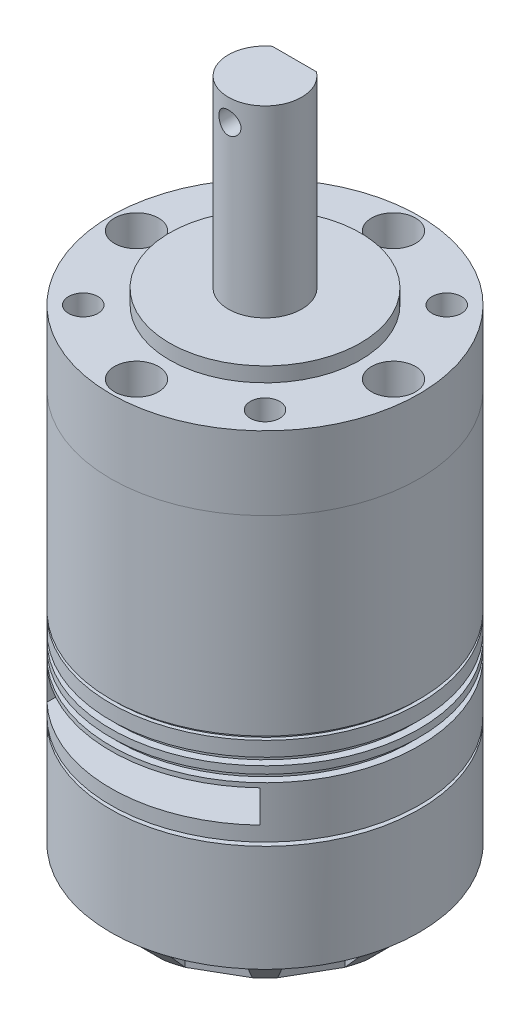
SolidWorks part; units mm, degrees
ref_plane "前视基准面" through (0, 0, 0) normal (0, 0, 1) x (1, 0, 0)
ref_plane "上视基准面" through (0, 0, 0) normal (0, 1, 0) x (1, 0, 0)
ref_plane "右视基准面" through (0, 0, 0) normal (1, 0, 0) x (0, 0, -1)
sketch "草图1" plane through (0, 0, 0) normal (0, 1, 0) x (1, 0, 0)
  circle A0 centre (0, 0) radius 21
  dimension "D1" = 42
extrude "凸台-拉伸1" add sketch "草图1" along normal blind 31
chamfer "倒角1" distance 3.5 angle 45 1 edges at (0, 0, 21)
sketch "草图2" plane through (0, 0, 0) normal (0, -1, 0) x (1, 0, 0)
  line L0 (3.35, -17.1764) -> (-3.35, -17.1764)
  line L1 (-3.35, -17.1764) -> (-3.85, -20.6441)
  line L2 (-3.85, -20.6441) -> (3.85, -20.6441) construction
  line L3 (3.85, -20.6441) -> (3.35, -17.1764)
  line L4 (-3.85, -20.6441) -> (-3.85, -22.4949)
  line L5 (-3.85, -22.4949) -> (3.85, -22.4949)
  line L6 (3.85, -22.4949) -> (3.85, -20.6441)
  line L7 (-6.9878, -19.8033) -> (-5.687, -16.5502)
  line L8 (-5.687, -16.5502) -> (-11.4894, -13.2002)
  line L9 (-11.4894, -13.2002) -> (-13.6562, -15.9533)
  line L10 (-13.6562, -15.9533) -> (-14.5816, -17.5562)
  line L11 (-14.5816, -17.5562) -> (-7.9133, -21.4062)
  line L12 (-7.9133, -21.4062) -> (-6.9878, -19.8033)
  line L13 (-13.6562, -15.9533) -> (-6.9878, -19.8033) construction
  line L14 (-15.9533, -13.6562) -> (-13.2002, -11.4894)
  line L15 (-13.2002, -11.4894) -> (-16.5502, -5.687)
  line L16 (-16.5502, -5.687) -> (-19.8033, -6.9878)
  line L17 (-19.8033, -6.9878) -> (-21.4062, -7.9133)
  line L18 (-21.4062, -7.9133) -> (-17.5562, -14.5816)
  line L19 (-17.5562, -14.5816) -> (-15.9533, -13.6562)
  line L20 (-19.8033, -6.9878) -> (-15.9533, -13.6562) construction
  line L21 (-20.6441, -3.85) -> (-17.1764, -3.35)
  line L22 (-17.1764, -3.35) -> (-17.1764, 3.35)
  line L23 (-17.1764, 3.35) -> (-20.6441, 3.85)
  line L24 (-20.6441, 3.85) -> (-22.4949, 3.85)
  line L25 (-22.4949, 3.85) -> (-22.4949, -3.85)
  line L26 (-22.4949, -3.85) -> (-20.6441, -3.85)
  line L27 (-20.6441, 3.85) -> (-20.6441, -3.85) construction
  line L28 (-19.8033, 6.9878) -> (-16.5502, 5.687)
  line L29 (-16.5502, 5.687) -> (-13.2002, 11.4894)
  line L30 (-13.2002, 11.4894) -> (-15.9533, 13.6562)
  line L31 (-15.9533, 13.6562) -> (-17.5562, 14.5816)
  line L32 (-17.5562, 14.5816) -> (-21.4062, 7.9133)
  line L33 (-21.4062, 7.9133) -> (-19.8033, 6.9878)
  line L34 (-15.9533, 13.6562) -> (-19.8033, 6.9878) construction
  line L35 (-13.6562, 15.9533) -> (-11.4894, 13.2002)
  line L36 (-11.4894, 13.2002) -> (-5.687, 16.5502)
  line L37 (-5.687, 16.5502) -> (-6.9878, 19.8033)
  line L38 (-6.9878, 19.8033) -> (-7.9133, 21.4062)
  line L39 (-7.9133, 21.4062) -> (-14.5816, 17.5562)
  line L40 (-14.5816, 17.5562) -> (-13.6562, 15.9533)
  line L41 (-6.9878, 19.8033) -> (-13.6562, 15.9533) construction
  line L42 (-3.85, 20.6441) -> (-3.35, 17.1764)
  line L43 (-3.35, 17.1764) -> (3.35, 17.1764)
  line L44 (3.35, 17.1764) -> (3.85, 20.6441)
  line L45 (3.85, 20.6441) -> (3.85, 22.4949)
  line L46 (3.85, 22.4949) -> (-3.85, 22.4949)
  line L47 (-3.85, 22.4949) -> (-3.85, 20.6441)
  line L48 (3.85, 20.6441) -> (-3.85, 20.6441) construction
  line L49 (6.9878, 19.8033) -> (5.687, 16.5502)
  line L50 (5.687, 16.5502) -> (11.4894, 13.2002)
  line L51 (11.4894, 13.2002) -> (13.6562, 15.9533)
  line L52 (13.6562, 15.9533) -> (14.5816, 17.5562)
  line L53 (14.5816, 17.5562) -> (7.9133, 21.4062)
  line L54 (7.9133, 21.4062) -> (6.9878, 19.8033)
  line L55 (13.6562, 15.9533) -> (6.9878, 19.8033) construction
  line L56 (15.9533, 13.6562) -> (13.2002, 11.4894)
  line L57 (13.2002, 11.4894) -> (16.5502, 5.687)
  line L58 (16.5502, 5.687) -> (19.8033, 6.9878)
  line L59 (19.8033, 6.9878) -> (21.4062, 7.9133)
  line L60 (21.4062, 7.9133) -> (17.5562, 14.5816)
  line L61 (17.5562, 14.5816) -> (15.9533, 13.6562)
  line L62 (19.8033, 6.9878) -> (15.9533, 13.6562) construction
  line L63 (20.6441, 3.85) -> (17.1764, 3.35)
  line L64 (17.1764, 3.35) -> (17.1764, -3.35)
  line L65 (17.1764, -3.35) -> (20.6441, -3.85)
  line L66 (20.6441, -3.85) -> (22.4949, -3.85)
  line L67 (22.4949, -3.85) -> (22.4949, 3.85)
  line L68 (22.4949, 3.85) -> (20.6441, 3.85)
  line L69 (20.6441, -3.85) -> (20.6441, 3.85) construction
  line L70 (19.8033, -6.9878) -> (16.5502, -5.687)
  line L71 (16.5502, -5.687) -> (13.2002, -11.4894)
  line L72 (13.2002, -11.4894) -> (15.9533, -13.6562)
  line L73 (15.9533, -13.6562) -> (17.5562, -14.5816)
  line L74 (17.5562, -14.5816) -> (21.4062, -7.9133)
  line L75 (21.4062, -7.9133) -> (19.8033, -6.9878)
  line L76 (15.9533, -13.6562) -> (19.8033, -6.9878) construction
  line L77 (13.6562, -15.9533) -> (11.4894, -13.2002)
  line L78 (11.4894, -13.2002) -> (5.687, -16.5502)
  line L79 (5.687, -16.5502) -> (6.9878, -19.8033)
  line L80 (6.9878, -19.8033) -> (7.9133, -21.4062)
  line L81 (7.9133, -21.4062) -> (14.5816, -17.5562)
  line L82 (14.5816, -17.5562) -> (13.6562, -15.9533)
  line L83 (6.9878, -19.8033) -> (13.6562, -15.9533) construction
  circle A0 centre (0, 0) radius 17.5 construction
  circle A1 centre (0, 0) radius 21 construction
  point P4 (0, -17.1764)
  point P80 (0, 0)
  dimension "D1" = 6.7
  dimension "D2" = 7.7
  dimension "D3" = 12
extrude "切除-拉伸1" cut sketch "草图2" against normal blind 3.5
sketch "草图3" plane through (0, 31, 0) normal (0, 1, 0) x (1, 0, 0)
  circle A0 centre (0, 0) radius 21
extrude "凸台-拉伸2" add sketch "草图3" along normal blind 26 separate body
sketch "草图4" plane through (0, 57, 0) normal (0, 1, 0) x (1, 0, 0)
  circle A0 centre (0, 0) radius 21
extrude "凸台-拉伸3" add sketch "草图4" along normal blind 10 separate body
sketch "草图5" plane through (0, 67, 0) normal (0, 1, 0) x (1, 0, 0)
  circle A0 centre (0, 0) radius 13
  dimension "D1" = 26
extrude "凸台-拉伸4" add sketch "草图5" along normal blind 2
sketch "草图6" plane through (0, 69, 0) normal (0, 1, 0) x (1, 0, 0)
  circle A0 centre (0, 0) radius 5
  dimension "D1" = 10
extrude "凸台-拉伸5" add sketch "草图6" along normal blind 25
sketch "草图7" plane through (0, 94, 0) normal (0, 1, 0) x (1, 0, 0)
  line L1 (-5.2834, 7.2706) -> (5.1995, 7.2706)
  line L2 (-5.2834, 7.2706) -> (-5.2834, 4)
  line L3 (-5.2834, 4) -> (5.1995, 4)
  line L4 (5.1995, 7.2706) -> (5.1995, 4)
  dimension "D1" = 4
extrude "D形面" cut sketch "草图7" against normal blind 20
ref_plane "基准面1" through (0, 31, 0) normal (0, -1, 0) x (-1, 0, 0)
sketch "草图8" plane through (0, 31, 0) normal (0, -1, 0) x (-1, 0, 0)
  circle A0 centre (0, 0) radius 21
  circle A1 centre (0, 0) radius 20.5
  dimension "D1" = 42
  dimension "D2" = 41
extrude "切除-拉伸3" cut sketch "草图8" along normal blind 0.5
ref_plane "基准面2" through (0, 26.5, 0) normal (0, -1, 0) x (-1, 0, 0)
sketch "草图9" plane through (0, 26.5, 0) normal (0, -1, 0) x (-1, 0, 0)
  circle A0 centre (0, 0) radius 21
  circle A1 centre (0, 0) radius 20
  dimension "D1" = 42
  dimension "D2" = 40
extrude "切除-拉伸4" cut sketch "草图9" along normal blind 1
ref_plane "基准面3" through (0, 27.5, 0) normal (0, -1, 0) x (-1, 0, 0)
sketch "草图10" plane through (0, 27.5, 0) normal (0, -1, 0) x (-1, 0, 0)
  circle A0 centre (0, 0) radius 21
  circle A1 centre (0, 0) radius 20
  dimension "D1" = 42
  dimension "D2" = 40
extrude "切除-拉伸5" cut sketch "草图10" against normal blind 1
ref_plane "基准面4" through (0, 18, 0) normal (0, -1, 0) x (-1, 0, 0)
sketch "草图11" plane through (0, 18, 0) normal (0, -1, 0) x (-1, 0, 0)
  circle A0 centre (0, 0) radius 21
  circle A1 centre (0, 0) radius 20
  dimension "D1" = 42
  dimension "D2" = 40
extrude "切除-拉伸6" cut sketch "草图11" against normal blind 0.5
ref_plane "基准面5" through (0, 24.9, 0) normal (0, 1, 0) x (1, 0, 0)
sketch "草图12" plane through (0, 24.9, 0) normal (0, 1, 0) x (1, 0, 0)
  line L1 (-14.5, -15.1905) -> (14.5, -15.1905)
  line L2 (-14.5, -15.1905) -> (-14.5, -28.1976)
  line L3 (-14.5, -28.1976) -> (14.5, -28.1976)
  line L4 (14.5, -15.1905) -> (14.5, -28.1976)
  circle A0 centre (0, 0) radius 21 construction
  dimension "D1" = 29
extrude "切除-拉伸7" cut sketch "草图12" against normal blind 4.4
sketch "草图13" plane through (0, 0, 15.1905) normal (0, 0, 1) x (1, 0, 0)
  line L1 (-14.5, 24.9) -> (14.5, 24.9)
  line L2 (-14.5, 24.9) -> (-14.5, 20.5)
  line L3 (-14.5, 20.5) -> (14.5, 20.5)
  line L4 (14.5, 24.9) -> (14.5, 20.5)
extrude "切除-拉伸8" cut sketch "草图13" against normal blind 5
sketch "草图14" plane through (0, 67, 0) normal (0, 1, 0) x (1, 0, 0)
  line L0 (0, 0) -> (12.3744, 12.3744) construction
  line L1 (0, 0) -> (17.5, 0) construction
  circle A0 centre (0, 0) radius 17.5 construction
  circle A1 centre (0, 17.5) radius 3
  circle A2 centre (-17.5, 0) radius 3
  circle A3 centre (0, -17.5) radius 3
  circle A4 centre (17.5, 0) radius 3
  circle A5 centre (12.3744, 12.3744) radius 2
  circle A6 centre (12.3744, -12.3744) radius 2
  circle A7 centre (-12.3744, -12.3744) radius 2
  circle A8 centre (-12.3744, 12.3744) radius 2
  point P22 (0, 0)
  dimension "D1" = 35
  dimension "D2" = 6
  dimension "D4" = 4
  dimension "D3" = 45
  dimension "D5" = 4
extrude "固定孔位" cut sketch "草图14" against normal blind 8
cosmetic thread "装饰螺纹线1" parameters "D2"=5
cosmetic thread "装饰螺纹线2" parameters "D2"=5
cosmetic thread "装饰螺纹线3" parameters "D2"=5
cosmetic thread "装饰螺纹线4" parameters "D2"=5
sketch "草图15" plane through (0, 0, 0) normal (0, -1, 0) x (1, 0, 0)
  circle A0 centre (0, 0) radius 3.5
  dimension "D1" = 7
extrude "凸台-拉伸6" add sketch "草图15" along normal blind 5
sketch "草图16" plane through (0, 0, 0) normal (0, -1, 0) x (1, 0, 0)
  circle A0 centre (-6.75, 0) radius 1.5
  circle A1 centre (6.75, 0) radius 1.5
  dimension "D3" = 3
  dimension "D1" = 13.5
  dimension "D2" = 6.75
extrude "切除-拉伸10" cut sketch "草图16" against normal blind 5
cosmetic thread "装饰螺纹线5" parameters "D2"=4
cosmetic thread "装饰螺纹线6" parameters "D2"=4
sketch "草图17" plane through (0, 0, -4) normal (0, 0, -1) x (-1, 0, 0)
  line L0 (0, 94) -> (0, -21.9241) construction
  line L1 (3, 94) -> (-3, 94) construction
  circle A0 centre (0, 91) radius 1.5
  dimension "D1" = 3
  dimension "D2" = 3
extrude "切除-拉伸11" cut sketch "草图17" against normal blind 10
